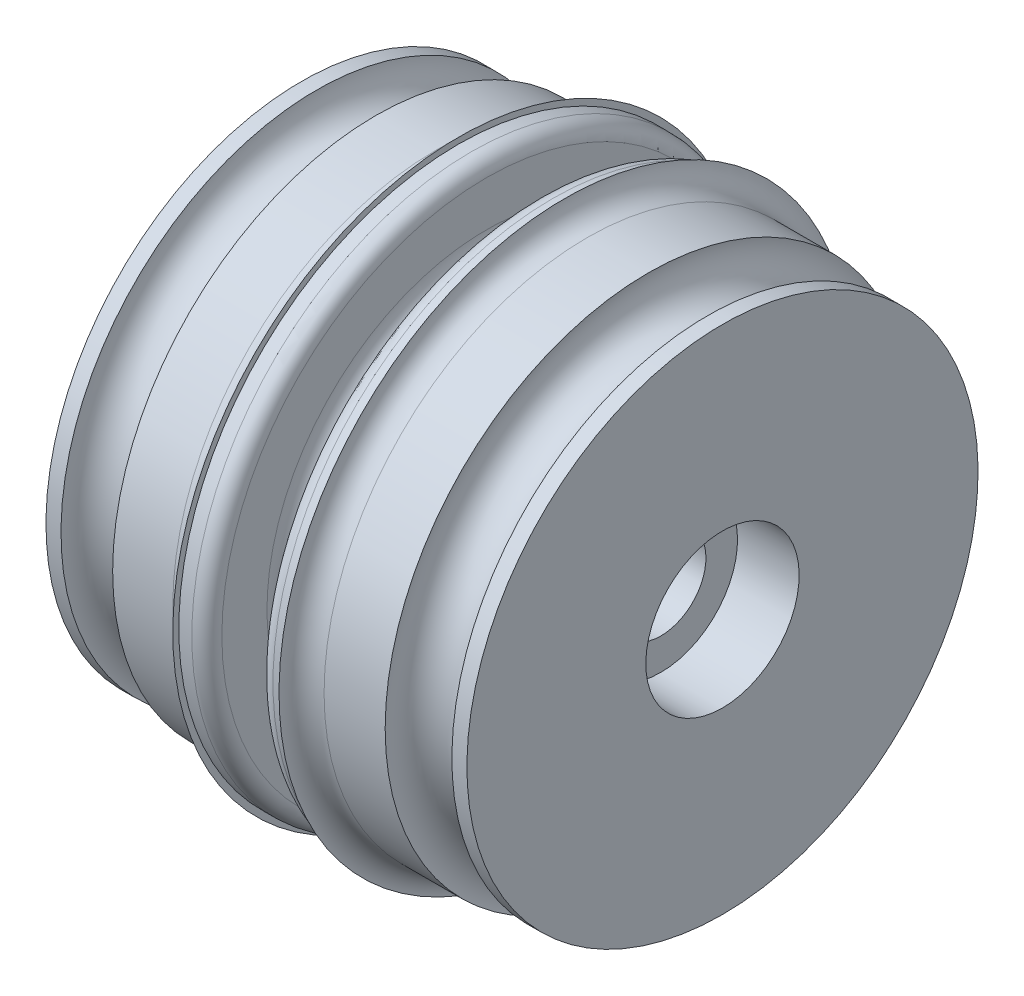
SolidWorks part; units mm, degrees
ref_plane "前视基准面" through (0, 0, 0) normal (0, 0, 1) x (1, 0, 0)
ref_plane "上视基准面" through (0, 0, 0) normal (0, 1, 0) x (1, 0, 0)
ref_plane "右视基准面" through (0, 0, 0) normal (1, 0, 0) x (0, 0, -1)
sketch "草图1" plane through (0, 0, 0) normal (0, 0, 1) x (1, 0, 0)
  line L0 (17.8004, 19) -> (17.8004, 18.6)
  line L1 (4.4004, 3) -> (24.2004, 3)
  line L2 (5.2369, 17.5) -> (9.2369, 17.5)
  line L3 (14.1004, 13.1) -> (14.5004, 13.1)
  line L4 (0.3004, 17) -> (1.3004, 17)
  line L5 (0.3004, 5.1) -> (4.4004, 5.1)
  line L6 (4.4004, 5.1) -> (4.4004, 3)
  line L7 (0, 0) -> (4.5, 0) construction
  line L8 (24.2004, 3) -> (24.2004, 5.1)
  line L9 (24.2004, 5.1) -> (28.3004, 5.1)
  line L10 (10.7369, 18.6) -> (10.7369, 19)
  line L12 (16.0004, 14.6) -> (16.0004, 17.6)
  line L13 (12.6004, 14.6) -> (12.6004, 17.6)
  line L14 (0.3004, 17) -> (0.3004, 5.1)
  line L15 (10.7369, 18.6) -> (11.6004, 18.6)
  line L16 (17.0004, 18.6) -> (17.8004, 18.6)
  line L18 (27.3004, 17) -> (28.3004, 17)
  line L19 (19.3004, 17.5) -> (23.3639, 17.5)
  line L34 (28.3004, 17) -> (28.3004, 5.1)
  arc A0 (1.3004, 17) -> (5.2369, 17.5) centre (3.3004, 17) ccw
  arc A1 (12.6004, 17.6) -> (11.6004, 18.6) centre (11.6004, 17.6) ccw
  arc A2 (23.3639, 17.5) -> (27.3004, 17) centre (25.3004, 17) ccw
  arc A3 (16.0004, 17.6) -> (17.0004, 18.6) centre (17.0004, 17.6) cw
  arc A4 (14.5004, 13.1) -> (16.0004, 14.6) centre (14.5004, 14.6) ccw
  arc A5 (14.1004, 13.1) -> (12.6004, 14.6) centre (14.1004, 14.6) cw
  arc A6 (17.8004, 19) -> (19.3004, 17.5) centre (19.3004, 19) ccw
  arc A7 (10.7369, 19) -> (9.2369, 17.5) centre (9.2369, 19) cw
  point P1 (0, 14)
  point P2 (2, 15)
  point P3 (4, 15.5)
  point P10 (4, 9.1086)
  point P20 (18.25, 9.1586)
  point P22 (17.8004, 16.2289)
  point P23 (18.25, 18.6076)
  point P24 (9.05, 9.1086)
  point P25 (9.05, 18.5576)
  point P31 (23.3, 15.5)
  point P32 (23.3, 9.1586)
  point P41 (10.7369, 17.5)
  point P44 (17.8004, 17.5)
  point P50 (16.0004, 18.6)
  dimension "D2" = 3
  dimension "D10" = 1
  dimension "D5" = 4.1
  dimension "D6" = 1.5
  dimension "D18" = 1.5
  dimension "D7" = 2
  dimension "D12" = 2
  dimension "D17" = 3
  dimension "D13" = 1
  dimension "D15" = 9.3
  dimension "D11" = 4
  dimension "D16" = 3
  dimension "D19" = 1.5
  dimension "D3" = 22
  dimension "D4" = 5.1
  dimension "D8" = 5.1
  dimension "D9" = 17
  dimension "D14" = 17
  dimension "D20" = 1
  dimension "D22" = 3.4
  dimension "D23" = 4.1
  dimension "D21" = 0.8
revolve "旋转1" add sketch "草图1" angle 360 about L7
